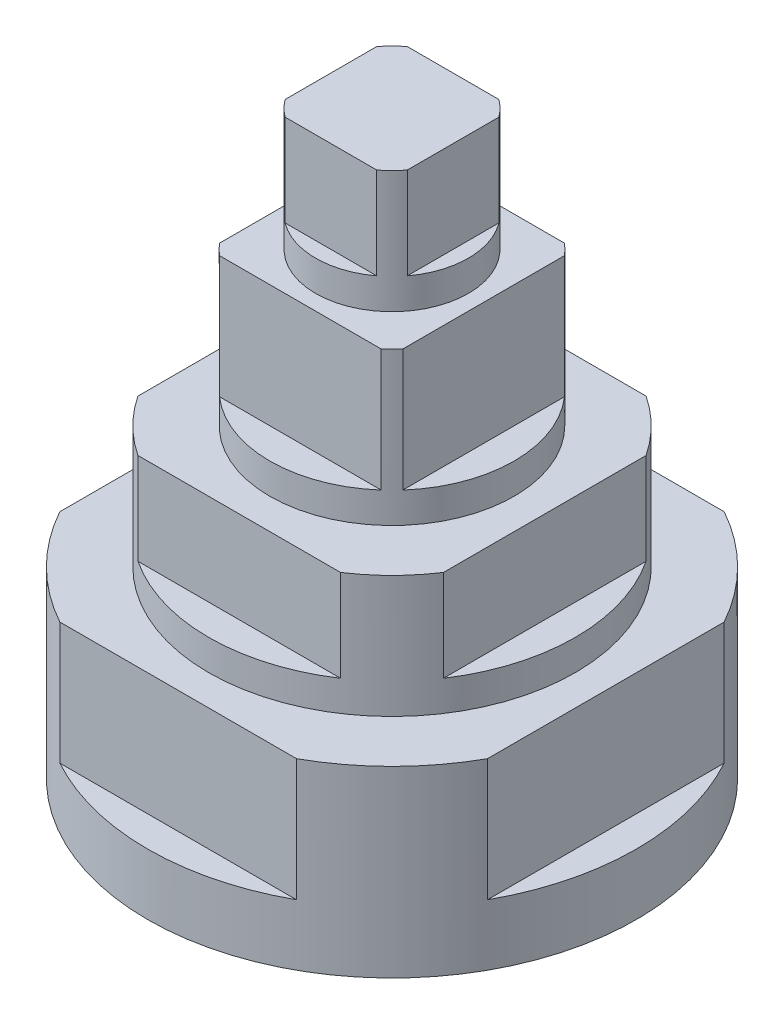
SolidWorks part; units mm, degrees
ref_plane "Front Plane" through (0, 0, 0) normal (0, 0, 1) x (1, 0, 0)
ref_plane "Top Plane" through (0, 0, 0) normal (0, 1, 0) x (1, 0, 0)
ref_plane "Right Plane" through (0, 0, 0) normal (1, 0, 0) x (0, 0, -1)
sketch "Sketch1" plane through (0, 0, 0) normal (0, 1, 0) x (1, 0, 0)
  circle A0 centre (0, 0) radius 40
  dimension "D1" = 80
extrude "Boss-Extrude1" add sketch "Sketch1" along normal blind 30
sketch "Sketch2" plane through (0, 30, 0) normal (0, 1, 0) x (1, 0, 0)
  circle A0 centre (0, 0) radius 30
  dimension "D1" = 60
extrude "Boss-Extrude2" add sketch "Sketch2" along normal blind 20
sketch "Sketch3" plane through (0, 50, 0) normal (0, 1, 0) x (1, 0, 0)
  circle A0 centre (0, 0) radius 20
  dimension "D1" = 40
extrude "Boss-Extrude3" add sketch "Sketch3" along normal blind 25
sketch "Sketch4" plane through (0, 75, 0) normal (0, 1, 0) x (1, 0, 0)
  circle A0 centre (0, 0) radius 12.5
  dimension "D1" = 25
extrude "Boss-Extrude4" add sketch "Sketch4" along normal blind 20
sketch "Sketch5" plane through (0, 95, 0) normal (0, 1, 0) x (1, 0, 0)
  line L1 (-10, -10) -> (10, -10)
  line L2 (-10, -10) -> (-10, 10)
  line L3 (-10, 10) -> (10, 10)
  line L4 (10, -10) -> (10, 10)
  line L5 (-10, -10) -> (10, 10) construction
  line L6 (-10, 10) -> (10, -10) construction
  point P0 (0, 0)
  dimension "D1" = 20
extrude "Cut-Extrude2" cut sketch "Sketch5" against normal blind 15 flip side to cut
sketch "Sketch6" plane through (0, 75, 0) normal (0, 1, 0) x (1, 0, 0)
  line L0 (-15, 15) -> (15, 15)
  line L1 (0, 0) -> (0, 15) construction
  line L2 (-15, 15) -> (-5.7759, 20.9496)
  line L3 (-5.7759, 20.9496) -> (14.2241, 20.9496)
  line L4 (14.2241, 20.9496) -> (15, 15)
  line L5 (20.9496, -14.2241) -> (15, -15)
  line L6 (15, 15) -> (15, -15)
  line L7 (15, 15) -> (20.9496, 5.7759)
  line L8 (20.9496, 5.7759) -> (20.9496, -14.2241)
  line L9 (-14.2241, -20.9496) -> (-15, -15)
  line L10 (15, -15) -> (-15, -15)
  line L11 (15, -15) -> (5.7759, -20.9496)
  line L12 (5.7759, -20.9496) -> (-14.2241, -20.9496)
  line L13 (-20.9496, 14.2241) -> (-15, 15)
  line L14 (-15, -15) -> (-15, 15)
  line L15 (-15, -15) -> (-20.9496, -5.7759)
  line L16 (-20.9496, -5.7759) -> (-20.9496, 14.2241)
  point P5 (0, 0)
  point P8 (-16.5906, -19.5329)
  point P9 (0, 0)
  point P22 (0, 0)
  point P23 (0, 0)
  point P24 (33.5467, -18.8472)
  point P25 (-21.1399, 13.8556)
  circle M3 centre (0, 0) radius 20
  dimension "D1" = 30
  dimension "D2" = 20
  dimension "D3" = 9.2241
  dimension "D4" = 6
  dimension "D5" = 15
  dimension "D7" = 15
  dimension "D8" = 15
  dimension "D6" = 4
extrude "Cut-Extrude7" cut sketch "Sketch6" against normal blind 20 contours L4 L3 L2 L0 M3 | L0 M3 | L6 M3 | L8 L7 L6 L5 M3 | L10 M3 | L12 L11 L10 L9 M3 | L14 M3 | L16 L15 L14 L13 M3
sketch "Sketch7" plane through (0, 0, 0) normal (0, 1, 0) x (1, 0, 0)
  line L0 (0, 0) -> (0, 25) construction
  line L1 (-24.9186, 25) -> (24.9186, 25)
  line L2 (25, 24.9186) -> (25, -24.9186)
  line L3 (24.9186, -25) -> (-24.9186, -25)
  line L4 (-25, -24.9186) -> (-25, 24.9186)
  arc A0 (-24.9186, 25) -> (24.9186, 25) centre (0, 0) cw
  arc A1 (25, 24.9186) -> (25, -24.9186) centre (0, 0) cw
  arc A2 (24.9186, -25) -> (-24.9186, -25) centre (0, 0) cw
  arc A3 (-25, -24.9186) -> (-25, 24.9186) centre (0, 0) cw
  point P6 (0, 25)
  dimension "D2" = 35.2978
  dimension "D1" = 25
  dimension "D3" = 4
extrude "Cut-Extrude8" cut sketch "Sketch7" against normal blind 15 from surface at 50 starting at face at (0, 50, 20)
ref_plane "Plane1" through (0, 30, 0) normal (0, 1, 0) x (1, 0, 0)
sketch "Sketch8" plane through (0, 30, 0) normal (0, 1, 0) x (1, 0, 0)
  line L0 (-35.7071, 35) -> (35.7071, 35)
  line L1 (0, 0) -> (0, 35) construction
  line L2 (35, 35.7071) -> (35, -35.7071)
  line L3 (35.7071, -35) -> (-35.7071, -35)
  line L4 (-35, -35.7071) -> (-35, 35.7071)
  arc A0 (-35.7071, 35) -> (35.7071, 35) centre (0, 0) cw
  arc A1 (35, 35.7071) -> (35, -35.7071) centre (0, 0) cw
  arc A2 (35.7071, -35) -> (-35.7071, -35) centre (0, 0) cw
  arc A3 (-35, -35.7071) -> (-35, 35.7071) centre (0, 0) cw
  dimension "D2" = 50
  dimension "D1" = 35
  dimension "D3" = 4
extrude "Cut-Extrude9" cut sketch "Sketch8" against normal blind 20 contours A0 L4 L0 L2 | A3 L3 L4 L0 | A1 L0 L2 L3 | A2 L2 L3 L4
